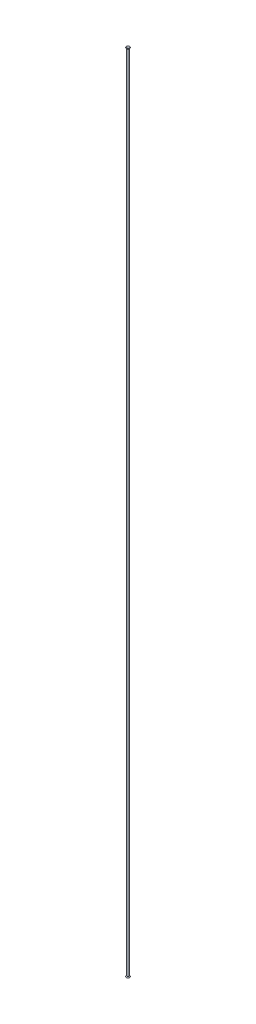
SolidWorks part; units mm, degrees
material "6061-T6 (SS)"
ref_plane "Front Plane" through (0, 0, 0) normal (0, 0, 1) x (1, 0, 0)
ref_plane "Top Plane" through (0, 0, 0) normal (0, 1, 0) x (1, 0, 0)
ref_plane "Right Plane" through (0, 0, 0) normal (1, 0, 0) x (0, 0, -1)
sketch "Sketch1" plane through (0, 0, 0) normal (0, 1, 0) x (1, 0, 0)
  circle A0 centre (0, 0) radius 3.175
  circle A1 centre (0, 0) radius 6.35
  dimension "D1" = 12.7
  dimension "D2" = 6.35
extrude "Boss-Extrude1" add sketch "Sketch1" along normal blind 4705.096
sketch "Sketch2" plane through (0, 0, 0) normal (0, 0, 1) x (1, 0, 0)
  line L0 (6.35, 4705.096) -> (10.4317, 4709.9604)
  line L1 (6.35, 4705.096) -> (-6.35, 4705.096) construction
  line L2 (6.35, 4705.096) -> (10.9567, 4705.096) construction
  line L3 (3.175, 4705.096) -> (8.5685, 4711.5238)
  line L4 (3.175, 4705.096) -> (-3.175, 4705.096) construction
  line L5 (10.4317, 4709.9604) -> (8.5685, 4711.5238)
  line L6 (6.35, 4705.096) -> (3.175, 4705.096)
  dimension "D1" = 50
  dimension "D2" = 6.35
  dimension "D3" = 2.4322
  dimension "D4" = 3.175
ref_axis "Axis1" through (0, 4946.8333, 0) along (0, -1, 0)
revolve "Revolve1" add sketch "Sketch2" angle 360 about axis through (0, 4946.8333, 0) along (0, -1, 0)
ref_plane "Plane1" through (0, 2352.548, 0) normal (0, 1, 0) x (1, 0, 0)
mirror "Mirror1" about plane through (0, 2352.548, 0) normal (0, 1, 0) of "Revolve1"
